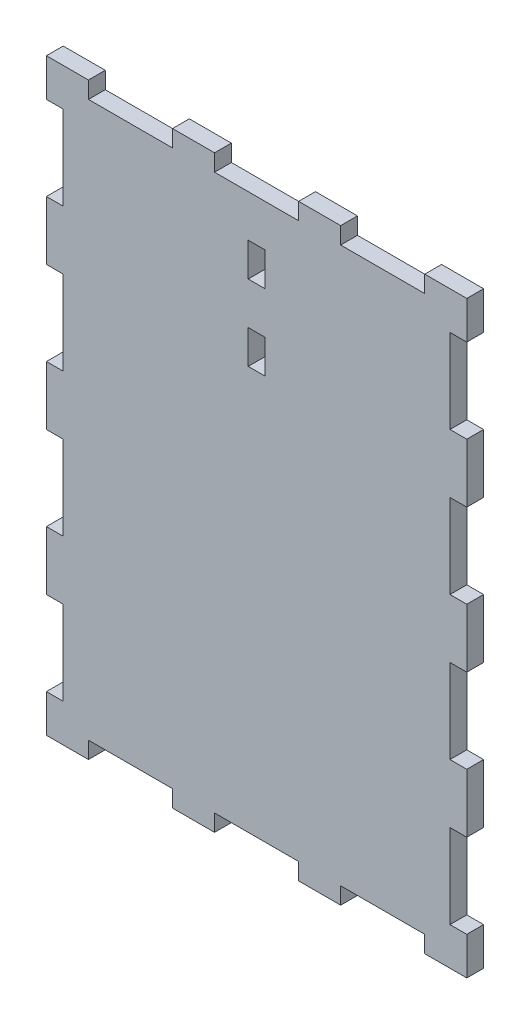
SolidWorks part; units mm, degrees
ref_plane "Front Plane" through (0, 0, 0) normal (0, 0, 1) x (1, 0, 0)
ref_plane "Top Plane" through (0, 0, 0) normal (0, 1, 0) x (1, 0, 0)
ref_plane "Right Plane" through (0, 0, 0) normal (1, 0, 0) x (0, 0, -1)
sketch "Sketch2" plane through (0, 0, 0) normal (0, 0, 1) x (1, 0, 0)
  line L1 (0, 0) -> (127, 0)
  line L2 (0, 0) -> (0, -177.8)
  line L3 (0, -177.8) -> (127, -177.8)
  line L4 (127, 0) -> (127, -177.8)
  dimension "D1" = 127
  dimension "D2" = 177.8
extrude "Boss-Extrude2" add sketch "Sketch2" along normal blind 5.08
sketch "Sketch3" plane through (0, 0, 0) normal (0, 0, -1) x (-1, 0, 0)
  line L0 (-127, -177.8) -> (-127, 0) construction
  line L1 (-127, -140.97) -> (-121.92, -140.97)
  line L2 (-127, -140.97) -> (-127, -166.37)
  line L3 (-127, -166.37) -> (-121.92, -166.37)
  line L4 (-121.92, -140.97) -> (-121.92, -166.37)
  line L5 (0, -177.8) -> (-127, -177.8) construction
  dimension "D1" = 5.08
  dimension "D2" = 25.4
  dimension "D3" = 11.43
extrude "Cut-Extrude1" cut sketch "Sketch3" against normal up to surface (5.08 mm away) up to face at (63.5, -88.9, 5.08)
pattern_linear "LPattern1" count 5 spacing 43.18 along (0, 1, 0) of "Cut-Extrude1"
sketch "Sketch4" plane through (0, 0, 0) normal (0, 0, -1) x (-1, 0, 0)
  line L0 (0, 0) -> (0, -177.8) construction
  line L1 (-5.08, -140.97) -> (0, -140.97)
  line L2 (-5.08, -140.97) -> (-5.08, -166.37)
  line L3 (-5.08, -166.37) -> (0, -166.37)
  line L4 (0, -140.97) -> (0, -166.37)
  line L7 (0, -177.8) -> (-127, -177.8) construction
  dimension "D1" = 5.08
  dimension "D2" = 11.43
  dimension "D3" = 25.4
extrude "Cut-Extrude2" cut sketch "Sketch4" against normal up to surface (5.08 mm away) up to face at (112.268, -88.9, 5.08)
pattern_linear "LPattern2" count 4 spacing 43.18 along (0, 1, 0) of "Cut-Extrude2"
sketch "Sketch5" plane through (0, 0, 0) normal (0, 0, -1) x (-1, 0, 0)
  line L0 (0, -177.8) -> (-127, -177.8) construction
  line L1 (-114.3, -172.72) -> (-88.9, -172.72)
  line L2 (-114.3, -172.72) -> (-114.3, -177.8)
  line L3 (-114.3, -177.8) -> (-88.9, -177.8)
  line L4 (-88.9, -172.72) -> (-88.9, -177.8)
  line L5 (-127, -177.8) -> (-127, -166.37) construction
  dimension "D1" = 5.08
  dimension "D2" = 12.7
  dimension "D3" = 25.4
extrude "Cut-Extrude3" cut sketch "Sketch5" against normal up to surface (5.08 mm away) up to face at (63.5, -88.9, 5.08)
pattern_linear "LPattern3" count 3 spacing 38.1 along (-1, 0, 0) of "Cut-Extrude3"
sketch "Sketch6" plane through (0, 0, 0) normal (0, 0, -1) x (-1, 0, 0)
  line L0 (-127, 0) -> (0, 0) construction
  line L1 (-12.7, -5.08) -> (-38.1, -5.08)
  line L2 (-12.7, -5.08) -> (-12.7, 0)
  line L3 (-12.7, 0) -> (-38.1, 0)
  line L4 (-38.1, -5.08) -> (-38.1, 0)
  line L5 (0, 0) -> (0, -11.43) construction
  dimension "D1" = 12.7
  dimension "D2" = 5.08
  dimension "D3" = 25.4
extrude "Cut-Extrude4" cut sketch "Sketch6" against normal up to surface (5.08 mm away) up to face at (63.5, -110.49, 5.08)
pattern_linear "LPattern4" count 3 spacing 38.1 along (1, 0, 0) of "Cut-Extrude4"
sketch "Sketch7" plane through (0, 0, 5.08) normal (0, 0, 1) x (1, 0, 0)
  line L1 (60.96, -17.78) -> (66.04, -17.78)
  line L2 (60.96, -17.78) -> (60.96, -27.94)
  line L3 (60.96, -27.94) -> (66.04, -27.94)
  line L4 (66.04, -17.78) -> (66.04, -27.94)
  line L5 (60.96, -40.64) -> (66.04, -40.64)
  line L6 (60.96, -40.64) -> (60.96, -50.8)
  line L7 (60.96, -50.8) -> (66.04, -50.8)
  line L8 (66.04, -40.64) -> (66.04, -50.8)
  line L9 (121.92, -36.83) -> (121.92, -11.43) construction
  line L10 (5.08, -11.43) -> (5.08, -36.83) construction
  line L12 (127, -54.61) -> (127, -36.83) construction
  line L13 (76.2, -5.08) -> (50.8, -5.08) construction
  dimension "D1" = 5.08
  dimension "D2" = 5.08
  dimension "D3" = 10.16
  dimension "D4" = 10.16
  dimension "D5" = 12.7
  dimension "D6" = 55.88
  dimension "D7" = 55.88
  dimension "D8" = 60.96
  dimension "D9" = 12.7
extrude "Cut-Extrude5" cut sketch "Sketch7" against normal up to surface (5.08 mm away) up to face at (63.5, -88.9, 0)
